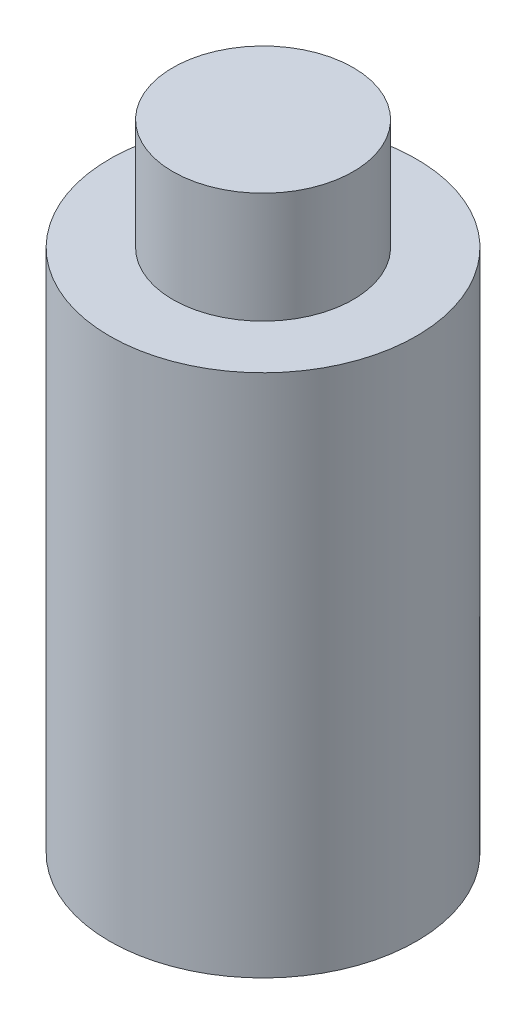
SolidWorks part; units mm, degrees
material "Delrin 2700 NC010, Low Viscosity Acetal Copolymer (SS)"
ref_plane "Front Plane" through (0, 0, 0) normal (0, 0, 1) x (1, 0, 0)
ref_plane "Top Plane" through (0, 0, 0) normal (0, 1, 0) x (1, 0, 0)
ref_plane "Right Plane" through (0, 0, 0) normal (1, 0, 0) x (0, 0, -1)
sketch "Sketch1" plane through (0, 0, 0) normal (0, 1, 0) x (1, 0, 0)
  circle A0 centre (0, 0) radius 27
  dimension "D1" = 54
extrude "Boss-Extrude1" add sketch "Sketch1" along normal blind 92.25
sketch "Sketch2" plane through (0, 92.25, 0) normal (0, 1, 0) x (1, 0, 0)
  circle A0 centre (0, 0) radius 15.875
  dimension "D1" = 31.75
extrude "Boss-Extrude2" add sketch "Sketch2" along normal blind 19.5
